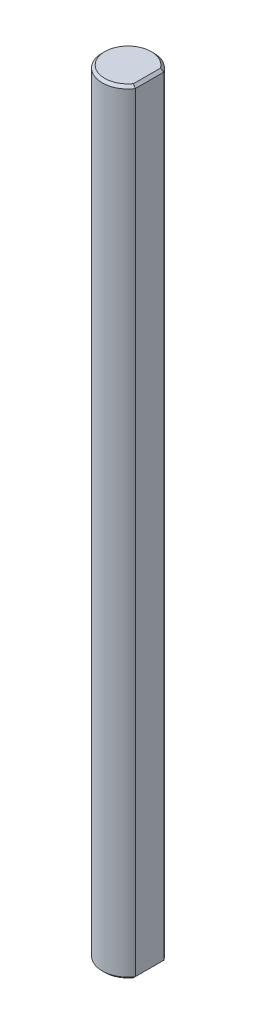
SolidWorks part; units mm, degrees
material "201 Annealed Stainless Steel (SS)"
ref_plane "Front Plane" through (0, 0, 0) normal (0, 0, 1) x (1, 0, 0)
ref_plane "Top Plane" through (0, 0, 0) normal (0, 1, 0) x (1, 0, 0)
ref_plane "Right Plane" through (0, 0, 0) normal (1, 0, 0) x (0, 0, -1)
sketch "Sketch1" plane through (0, 0, 0) normal (0, 1, 0) x (1, 0, 0)
  line L0 (2.5, 1.6583) -> (2.5, -1.6583)
  line L1 (2.5, 0) -> (-3, 0) construction
  arc A0 (2.5, 1.6583) -> (2.5, -1.6583) centre (0, 0) ccw
  dimension "D1" = 3
  dimension "D2" = 5.5
extrude "Boss-Extrude1" add sketch "Sketch1" along normal blind 90
chamfer "Chamfer1" distance 0.3 angle 45 4 edges at (2.5, 0, 0) (-3, 0, 0) (2.5, 90, 0) (-3, 90, 0)
